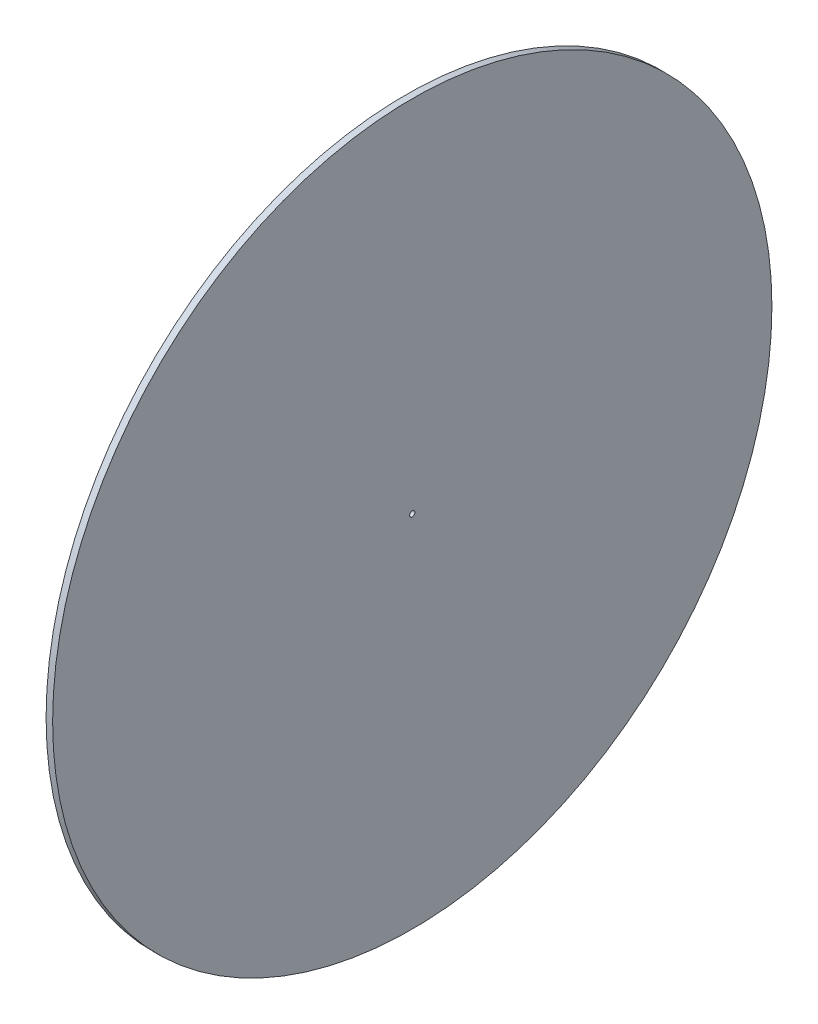
SolidWorks part; units mm, degrees
ref_plane "Plan de face" through (0, 0, 0) normal (0, 0, 1) x (1, 0, 0)
ref_plane "Plan de dessus" through (0, 0, 0) normal (0, 1, 0) x (1, 0, 0)
ref_plane "Plan de droite" through (0, 0, 0) normal (1, 0, 0) x (0, 0, -1)
sketch "Esquisse2" plane through (0, 0, 0) normal (1, 0, 0) x (0, 0, -1)
  circle A0 centre (0, 0) radius 165
extrude "Boss.-Extru.1" add sketch "Esquisse2" along normal blind 3
sketch "Esquisse3" plane through (3, 0, 0) normal (1, 0, 0) x (0, 0, -1)
  line L1 (0, 0) -> (5, 0)
  line L2 (0, 0) -> (0, 5)
  line L3 (0, 5) -> (5, 5)
  line L4 (5, 0) -> (5, 5)
  dimension "D1" = 5
  dimension "D2" = 5
extrude "Enlèv. mat.-Extru.1" [suppressed] cut sketch "Esquisse3" against normal blind 13
sketch "Esquisse4" plane through (3, 0, 0) normal (1, 0, 0) x (0, 0, -1)
  circle A0 centre (0, 0) radius 1.2
  point P3 (0, 0)
  point P4 (0, 0)
  point P5 (0, 0)
  point P6 (0, 0)
extrude "Enlèv. mat.-Extru.2" cut sketch "Esquisse4" against normal blind 10 contours A0
